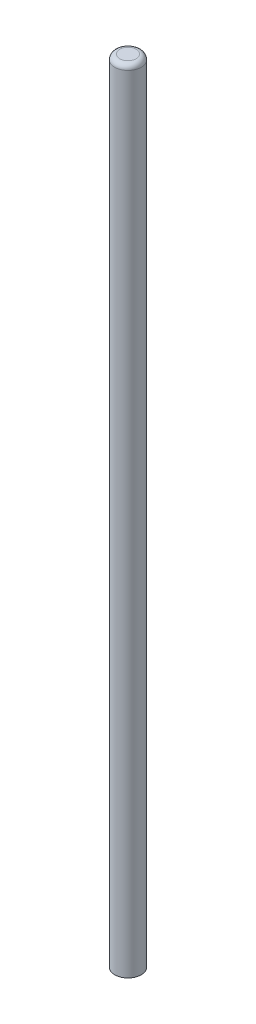
SolidWorks part; units mm, degrees
material "AISI 1045 Steel, cold drawn"
ref_plane "Front Plane" through (0, 0, 0) normal (0, 0, 1) x (1, 0, 0)
ref_plane "Top Plane" through (0, 0, 0) normal (0, 1, 0) x (1, 0, 0)
ref_plane "Right Plane" through (0, 0, 0) normal (1, 0, 0) x (0, 0, -1)
sketch "Sketch1" plane through (0, 0, 0) normal (0, 1, 0) x (1, 0, 0)
  circle A0 centre (0, 0) radius 2
  dimension "D1" = 4
extrude "Boss-Extrude1" add sketch "Sketch1" along normal blind 120
fillet "Fillet1" radius 0.75 1 edges at (0, 120, 2)
